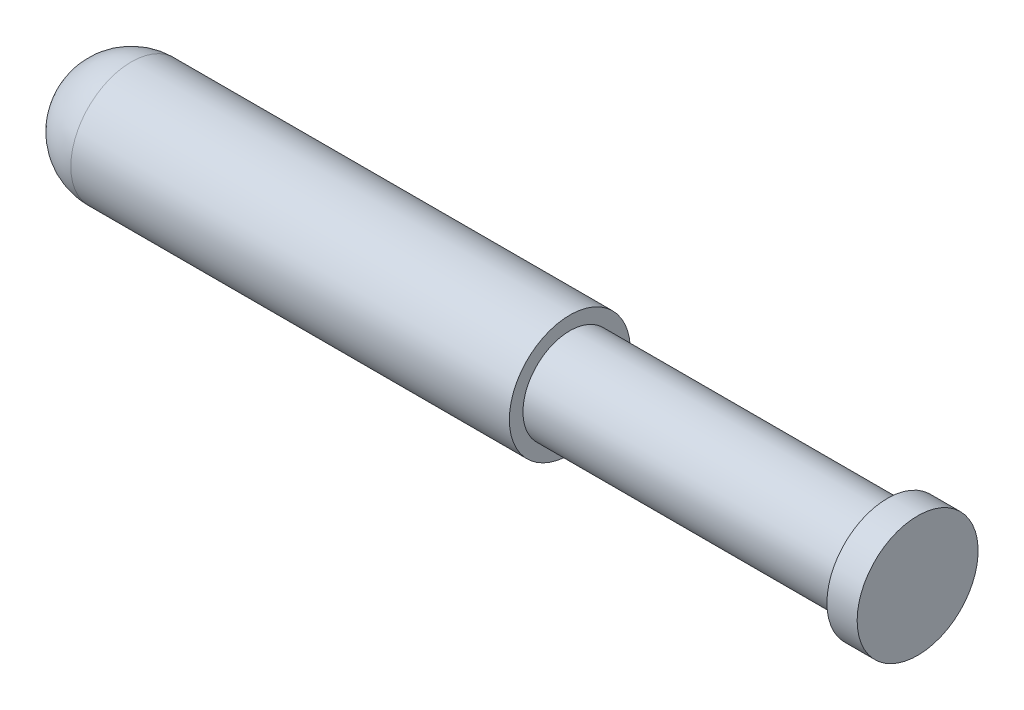
SolidWorks part; units mm, degrees
ref_plane "Front Plane" through (0, 0, 0) normal (0, 0, 1) x (1, 0, 0)
ref_plane "Top Plane" through (0, 0, 0) normal (0, 1, 0) x (1, 0, 0)
ref_plane "Right Plane" through (0, 0, 0) normal (1, 0, 0) x (0, 0, -1)
sketch "Sketch1" plane through (0, 0, 0) normal (0, 0, 1) x (1, 0, 0)
  line L0 (0, 0) -> (68.0954, 0) construction
  line L1 (0, 0) -> (0, 4)
  line L2 (0, 4) -> (33, 4)
  line L3 (33, 4) -> (33, 3.1)
  line L4 (33, 3.1) -> (54, 3.1)
  line L5 (54, 3.1) -> (54, 4)
  line L6 (54, 4) -> (56, 4)
  line L7 (56, 4) -> (56, 0)
  line L8 (56, 0) -> (0, 0)
  dimension "D5" = 2
  dimension "D1" = 56
  dimension "D2" = 4
  dimension "D3" = 3.1
  dimension "D4" = 33
  dimension "D6" = 4
revolve "Revolve1" add sketch "Sketch1" angle 360 about L0
fillet "Fillet1" radius 4 1 edges at (0, 0, 4)
